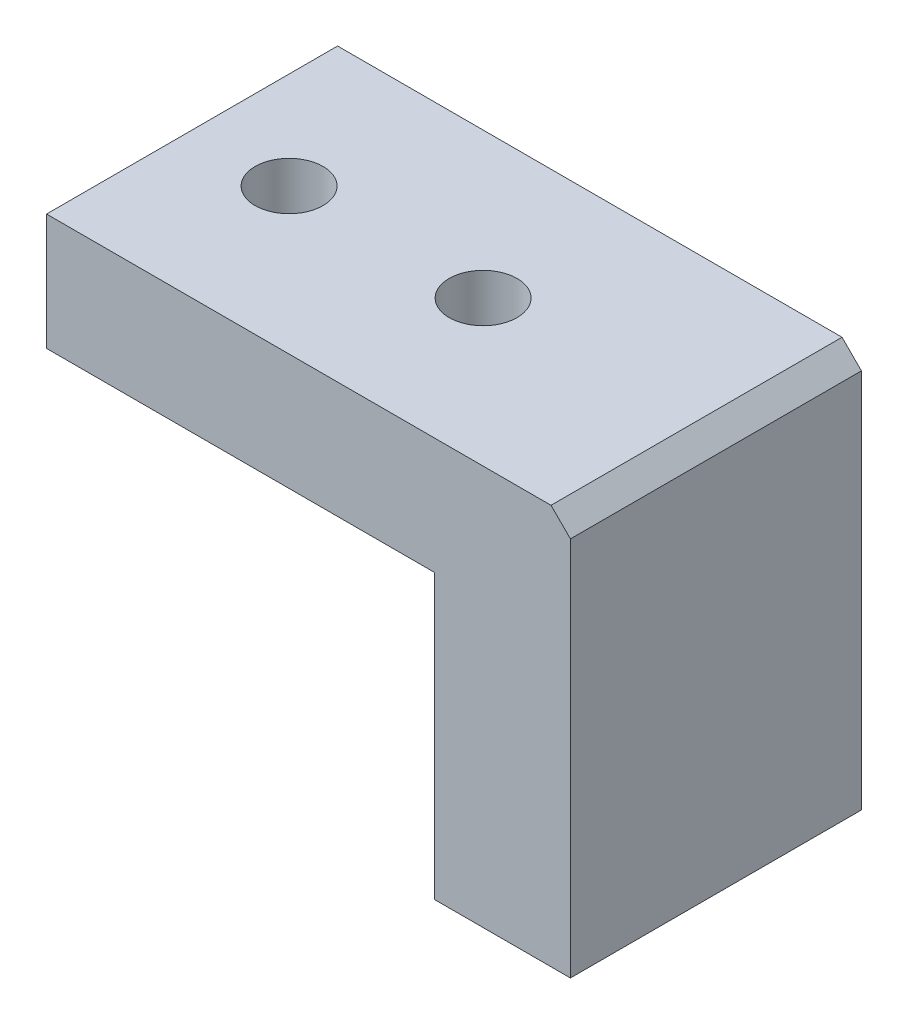
SolidWorks part; units mm, degrees
ref_plane "Front Plane" through (0, 0, 0) normal (0, 0, 1) x (1, 0, 0)
ref_plane "Top Plane" through (0, 0, 0) normal (0, 1, 0) x (1, 0, 0)
ref_plane "Right Plane" through (0, 0, 0) normal (1, 0, 0) x (0, 0, -1)
sketch "Sketch1" plane through (0, 0, 0) normal (0, 0, 1) x (1, 0, 0)
  line L0 (-9.6622, 6) -> (17.3378, 6)
  line L1 (17.3378, 6) -> (17.3378, -14.6)
  line L2 (17.3378, -14.6) -> (10.3378, -14.6)
  line L3 (10.3378, -14.6) -> (10.3378, 0)
  line L4 (10.3378, 0) -> (-9.6622, 0)
  line L5 (-9.6622, 0) -> (-9.6622, 6)
  dimension "D1" = 27
  dimension "D2" = 6
  dimension "D3" = 20.6
  dimension "D4" = 7
extrude "Boss-Extrude1" add sketch "Sketch1" along normal blind 15
chamfer "Chamfer1" distance 1 angle 45 1 edges at (17.3378, 6, 7.5)
sketch "Sketch2" plane through (0, 0, 0) normal (0, -1, 0) x (1, 0, 0)
  line L0 (-9.6622, 15) -> (-9.6622, 0) construction
  line L1 (-9.6622, 15) -> (10.3378, 15) construction
  circle A0 centre (-4.6622, 7.5) radius 1.75
  circle A1 centre (5.3378, 7.5) radius 1.75
  point P4 (0, 0)
  dimension "D1" = 3.5
  dimension "D2" = 10
  dimension "D3" = 5
  dimension "D4" = 7.5
extrude "Cut-Extrude1" cut sketch "Sketch2" against normal through all
